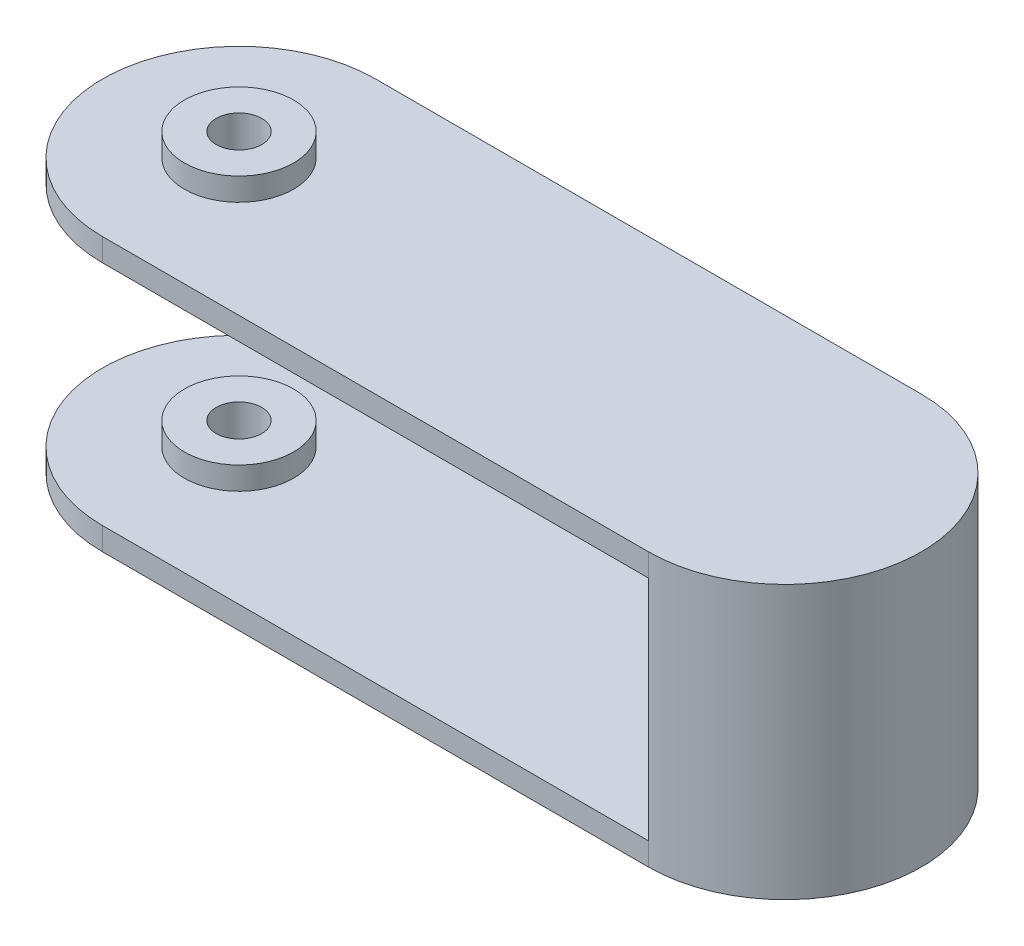
SolidWorks part; units mm, degrees
ref_plane "Front Plane" through (0, 0, 0) normal (0, 0, 1) x (1, 0, 0)
ref_plane "Top Plane" through (0, 0, 0) normal (0, 1, 0) x (1, 0, 0)
ref_plane "Right Plane" through (0, 0, 0) normal (1, 0, 0) x (0, 0, -1)
sketch "Sketch1" plane through (0, 0, 0) normal (0, 1, 0) x (1, 0, 0)
  line L0 (-30, 0) -> (30, 0) construction
  line L1 (-30, 15) -> (30, 15)
  line L2 (-30, -15) -> (30, -15)
  arc A0 (-30, 15) -> (-30, -15) centre (-30, 0) ccw
  arc A1 (30, -15) -> (30, 15) centre (30, 0) ccw
  point P3 (0, 0)
  dimension "D1" = 30
  dimension "D2" = 60
extrude "Boss-Extrude1" add sketch "Sketch1" along normal blind 30 contours L2 A1 L1 A0
sketch "Sketch4" plane through (0, 30, 0) normal (0, 1, 0) x (1, 0, 0)
  line L0 (-30, 15) -> (30, 15) construction
  circle A0 centre (-30, 0) radius 2.5
  dimension "D1" = 5
  dimension "D2" = 15
  dimension "D3" = 30
extrude "Cut-Extrude1" cut sketch "Sketch4" against normal blind 46 and the other way through all
sketch "Sketch6" plane through (0, 0, 15) normal (0, 0, 1) x (1, 0, 0)
  line L1 (-45, 27.5) -> (30, 27.5)
  line L2 (-45, 27.5) -> (-45, 2.5)
  line L3 (-45, 2.5) -> (30, 2.5)
  line L4 (30, 27.5) -> (30, 2.5)
  line L5 (-30, 0) -> (30, 0) construction
  line L6 (-30, 30) -> (30, 30) construction
  line L8 (-45, 30) -> (-45, 0) construction
  dimension "D1" = 25
  dimension "D2" = 2.5
  dimension "D3" = 75
  dimension "D4" = 0
extrude "Cut-Extrude3" cut sketch "Sketch6" against normal through all
sketch "Sketch7" plane through (0, 30, 0) normal (0, 1, 0) x (1, 0, 0)
  circle A0 centre (-30, 0) radius 6
  circle A1 centre (-30, 0) radius 2.5
extrude "Boss-Extrude2" add sketch "Sketch7" along normal blind 2.5
sketch "Sketch8" plane through (0, 0, 0) normal (0, -1, 0) x (1, 0, 0)
  circle A0 centre (-30, 0) radius 6
  circle A1 centre (-30, 0) radius 2.5
  circle M2 centre (-30, 0) radius 2.5
extrude "Boss-Extrude3" add sketch "Sketch8" against normal blind 5 contours A0 M2
